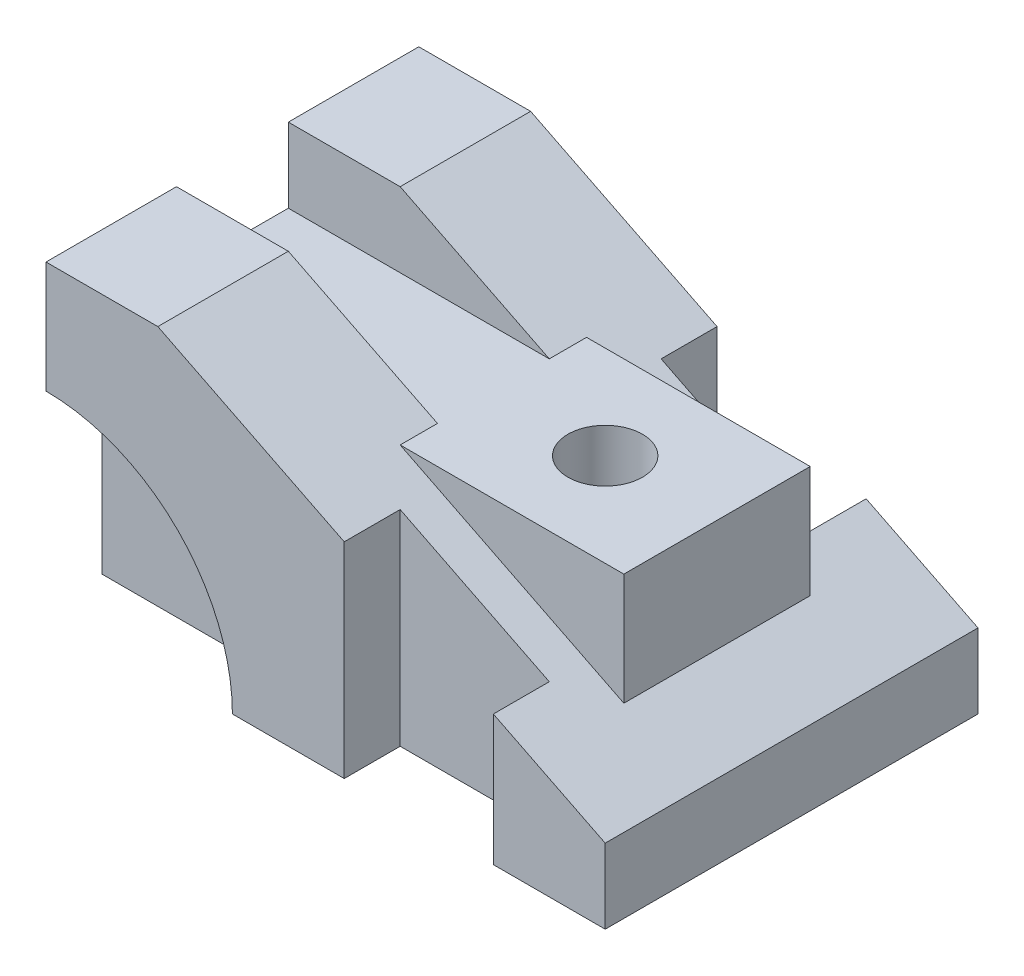
SolidWorks part; units mm, degrees
ref_plane "Front Plane" through (0, 0, 0) normal (0, 0, 1) x (1, 0, 0)
ref_plane "Top Plane" through (0, 0, 0) normal (0, 1, 0) x (1, 0, 0)
ref_plane "Right Plane" through (0, 0, 0) normal (1, 0, 0) x (0, 0, -1)
sketch "Sketch1" plane through (0, 0, 0) normal (0, 0, 1) x (1, 0, 0)
  line L0 (-52.0619, 38.6082) -> (-52.0619, -41.3918)
  line L1 (-52.0619, -41.3918) -> (97.9381, -41.3918)
  line L2 (97.9381, -41.3918) -> (97.9381, -21.3918)
  line L3 (97.9381, -21.3918) -> (-22.0619, 38.6082)
  line L4 (-22.0619, 38.6082) -> (-52.0619, 38.6082)
  dimension "D1" = 150
  dimension "D2" = 20
  dimension "D3" = 80
  dimension "D4" = 30
extrude "Boss-Extrude1" add sketch "Sketch1" against normal blind 100
sketch "Sketch2" plane through (0, 0, 0) normal (0, 0, 1) x (1, 0, 0)
  circle A0 centre (-52.0619, -41.3918) radius 50
  dimension "D1" = 100
extrude "Cut-Extrude1" cut sketch "Sketch2" against normal blind 15
sketch "Sketch3" plane through (0, 0, -100) normal (0, 0, -1) x (-1, 0, 0)
  circle A0 centre (52.0619, -41.3918) radius 50
  dimension "D1" = 100
extrude "Cut-Extrude2" cut sketch "Sketch3" against normal blind 15
sketch "Sketch4" plane through (0, -41.3918, 0) normal (0, -1, 0) x (1, 0, 0)
  line L0 (-2.0619, 0) -> (97.9381, 0) construction
  line L1 (67.9381, 0) -> (27.9381, 0)
  line L2 (67.9381, 0) -> (67.9381, -15)
  line L3 (67.9381, -15) -> (27.9381, -15)
  line L4 (27.9381, 0) -> (27.9381, -15)
  line L5 (97.9381, -100) -> (97.9381, 0) construction
  line L6 (-2.0619, -100) -> (97.9381, -100) construction
  line L7 (27.9381, -100) -> (67.9381, -100)
  line L8 (27.9381, -100) -> (27.9381, -85)
  line L9 (27.9381, -85) -> (67.9381, -85)
  line L10 (67.9381, -100) -> (67.9381, -85)
  dimension "D1" = 15
  dimension "D2" = 30
  dimension "D3" = 40
  dimension "D4" = 40
  dimension "D5" = 30
  dimension "D6" = 15
extrude "Cut-Extrude3" cut sketch "Sketch4" against normal blind 75
sketch "Sketch5" plane through (0, -41.3918, 0) normal (0, -1, 0) x (1, 0, 0)
  line L0 (67.9381, -100) -> (97.9381, -100) construction
  line L1 (17.9381, -25) -> (77.9381, -25)
  line L2 (17.9381, -25) -> (17.9381, -75)
  line L3 (17.9381, -75) -> (77.9381, -75)
  line L4 (77.9381, -25) -> (77.9381, -75)
  line L5 (97.9381, -100) -> (97.9381, 0) construction
  dimension "D1" = 50
  dimension "D2" = 25
  dimension "D3" = 20
  dimension "D4" = 60
extrude "Boss-Extrude2" add sketch "Sketch5" against normal blind 60
sketch "Sketch7" plane through (-52.0619, 0, 0) normal (-1, 0, 0) x (0, 0, 1)
  line L0 (-100, 38.6082) -> (0, 38.6082) construction
  line L1 (-65, 38.6082) -> (-35, 38.6082)
  line L2 (-65, 38.6082) -> (-65, 18.6082)
  line L3 (-65, 18.6082) -> (-35, 18.6082)
  line L4 (-35, 38.6082) -> (-35, 18.6082)
  line L5 (-100, 38.6082) -> (-100, 8.6082) construction
  dimension "D1" = 30
  dimension "D2" = 20
  dimension "D3" = 35
extrude "Cut-Extrude4" cut sketch "Sketch7" against normal blind 100
sketch "Sketch8" plane through (0, 18.6082, 0) normal (0, 1, 0) x (1, 0, 0)
  line L0 (77.9381, 75) -> (77.9381, 25) construction
  line L1 (77.9381, 75) -> (17.9381, 75) construction
  circle A0 centre (47.9381, 50) radius 10
  dimension "D1" = 20
  dimension "D2" = 30
  dimension "D3" = 25
extrude "Cut-Extrude5" cut sketch "Sketch8" against normal blind 100
